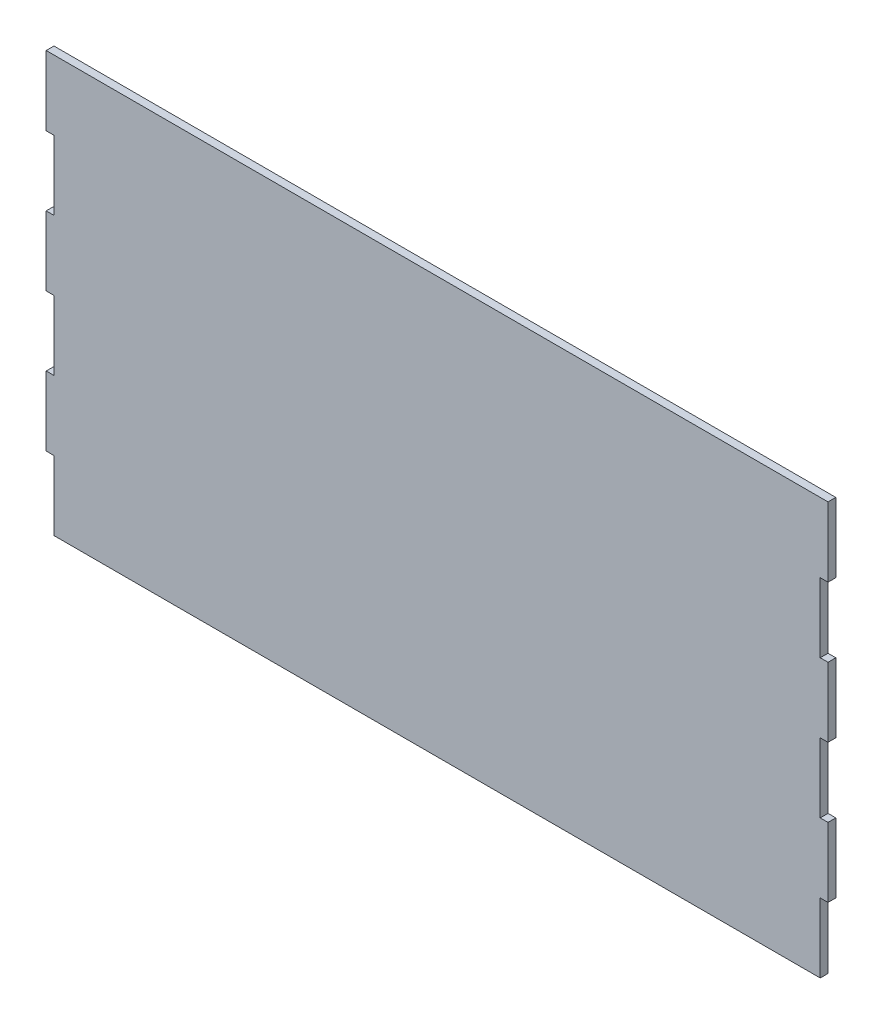
SolidWorks part; units mm, degrees
ref_plane "Front Plane" through (0, 0, 0) normal (0, 0, 1) x (1, 0, 0)
ref_plane "Top Plane" through (0, 0, 0) normal (0, 1, 0) x (1, 0, 0)
ref_plane "Right Plane" through (0, 0, 0) normal (1, 0, 0) x (0, 0, -1)
sketch "Sketch2" plane through (0, 0, 0) normal (0, 0, 1) x (1, 0, 0)
  line L5 (-147.5372, -23.2572) -> (147.5372, -23.2572)
  line L25 (0, 113.2488) -> (0, -33.3516) construction
  line L51 (-150.5372, 137.0213) -> (-147.5372, 137.0213)
  line L52 (-150.5372, 137.0213) -> (-150.5372, 110.2428)
  line L53 (-150.5372, 110.2428) -> (-150.5372, 137.0213) construction
  line L54 (-150.5372, 110.2428) -> (-147.5372, 110.2428) construction
  line L55 (-150.5372, 110.2428) -> (-147.5372, 110.2428)
  line L56 (-147.5372, 110.2428) -> (-147.5372, 83.5428)
  line L57 (-147.5372, 83.5428) -> (-150.5372, 83.5428)
  line L58 (-150.5372, 83.5428) -> (-150.5372, 56.8428)
  line L59 (-150.5372, 56.8428) -> (-147.5372, 56.8428)
  line L60 (-147.5372, 56.8428) -> (-147.5372, 30.1428)
  line L61 (-147.5372, 30.1428) -> (-150.5372, 30.1428)
  line L62 (-150.5372, 30.1428) -> (-150.5372, 3.4428)
  line L63 (-150.5372, 3.4428) -> (-147.5372, 3.4428)
  line L64 (-147.5372, 3.4428) -> (-147.5372, -23.2572)
  line L65 (147.5372, 3.4428) -> (147.5372, -23.2572)
  line L66 (150.5372, 3.4428) -> (147.5372, 3.4428)
  line L67 (150.5372, 30.1428) -> (150.5372, 3.4428)
  line L68 (147.5372, 30.1428) -> (150.5372, 30.1428)
  line L69 (147.5372, 56.8428) -> (147.5372, 30.1428)
  line L70 (150.5372, 56.8428) -> (147.5372, 56.8428)
  line L71 (150.5372, 83.5428) -> (150.5372, 56.8428)
  line L72 (147.5372, 83.5428) -> (150.5372, 83.5428)
  line L73 (147.5372, 110.2428) -> (147.5372, 83.5428)
  line L74 (150.5372, 110.2428) -> (147.5372, 110.2428)
  line L75 (150.5372, 137.0213) -> (150.5372, 110.2428)
  line L76 (150.5372, 137.0213) -> (147.5372, 137.0213)
  line L77 (-147.5372, 137.0213) -> (147.5372, 137.0213)
  point P0 (0, 0)
  point P9 (0, 0)
  point P17 (0, 74.9999)
extrude "Boss-Extrude2" add sketch "Sketch2" along normal blind 3
